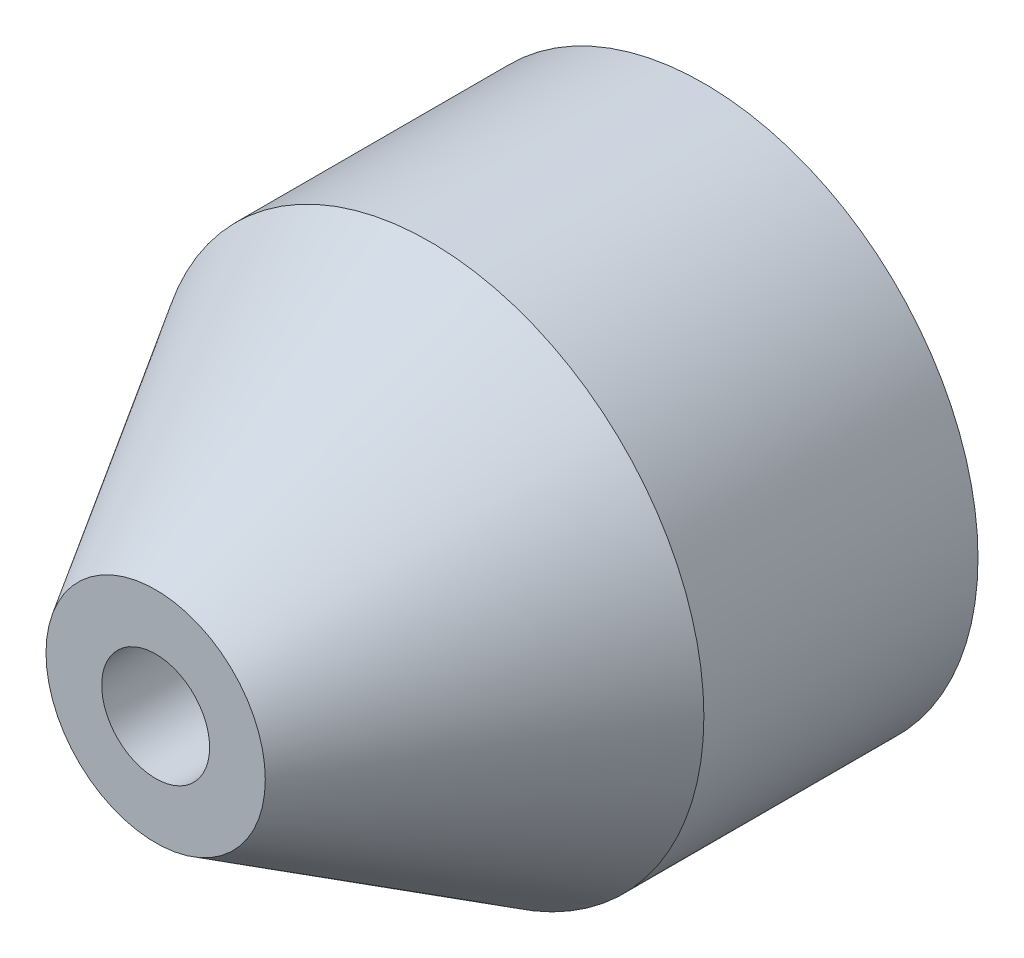
SolidWorks part; units mm, degrees
material "6061-T6 (SS)"
ref_plane "Front Plane" through (0, 0, 0) normal (0, 0, 1) x (1, 0, 0)
ref_plane "Top Plane" through (0, 0, 0) normal (0, 1, 0) x (1, 0, 0)
ref_plane "Right Plane" through (0, 0, 0) normal (1, 0, 0) x (0, 0, -1)
sketch "Sketch1" plane through (0, 0, 0) normal (0, 0, 1) x (1, 0, 0)
  circle A0 centre (0, 0) radius 6.35
  dimension "D1" = 12.7
extrude "Boss-Extrude1" add sketch "Sketch1" along normal blind 12.7
hole_wizard "M3x0.5 Tapped Hole1" positions "Sketch3" profile "Sketch2" tap size "M3x0.5" standard "ANSI Metric" end condition through all
sketch "Sketch3" plane through (0, 0, 12.7) normal (0, 0, 1) x (1, 0, 0)
  point P0 (0, 0)
sketch "Sketch2" plane through (0, 0, 12.7) normal (1, 0, 0) x (0, -1, 0)
  line L0 (0, 0) -> (0, 12.7)
  line L1 (0, 12.7) -> (1.25, 12.7)
  line L2 (1.25, 12.7) -> (1.25, 0)
  line L5 (1.25, 0) -> (0, 0)
  line L11 (0, -6.35) -> (0, 107.95) construction
  dimension "Thru Tap Drill Dia." = 2.5
  dimension "Thru Tap Drill Depth" = 12.7
cosmetic thread "Hole Thread1"
hole_wizard "#6-32 Tapped Hole1" positions "Sketch5" profile "Sketch6" tap size "#6-32" standard "ANSI Inch"
sketch "Sketch5" plane through (0, 0, 0) normal (0, 0, -1) x (-1, 0, 0)
  point P0 (0, 0)
sketch "Sketch6" plane through (0, 0, 0) normal (1, 0, 0) x (0, 1, 0)
  line L0 (0, 0) -> (0, 10.2107)
  line L1 (0, 10.2107) -> (1.3525, 9.398)
  line L2 (1.3525, 9.398) -> (1.3525, 0)
  line L5 (1.3525, 0) -> (0, 0)
  line L10 (0, 10.2107) -> (-1.3525, 9.398) construction
  line L11 (0, -6.35) -> (0, 107.95) construction
  dimension "Tap Drill Dia." = 2.7051
  dimension "Tap Drill Depth" = 9.398
  dimension "Drill Angle" = 118
cosmetic thread "Hole Thread2"
chamfer "Chamfer1" distance 6.35 distance2 3.81 1 edges at (6.35, 0, 12.7)
